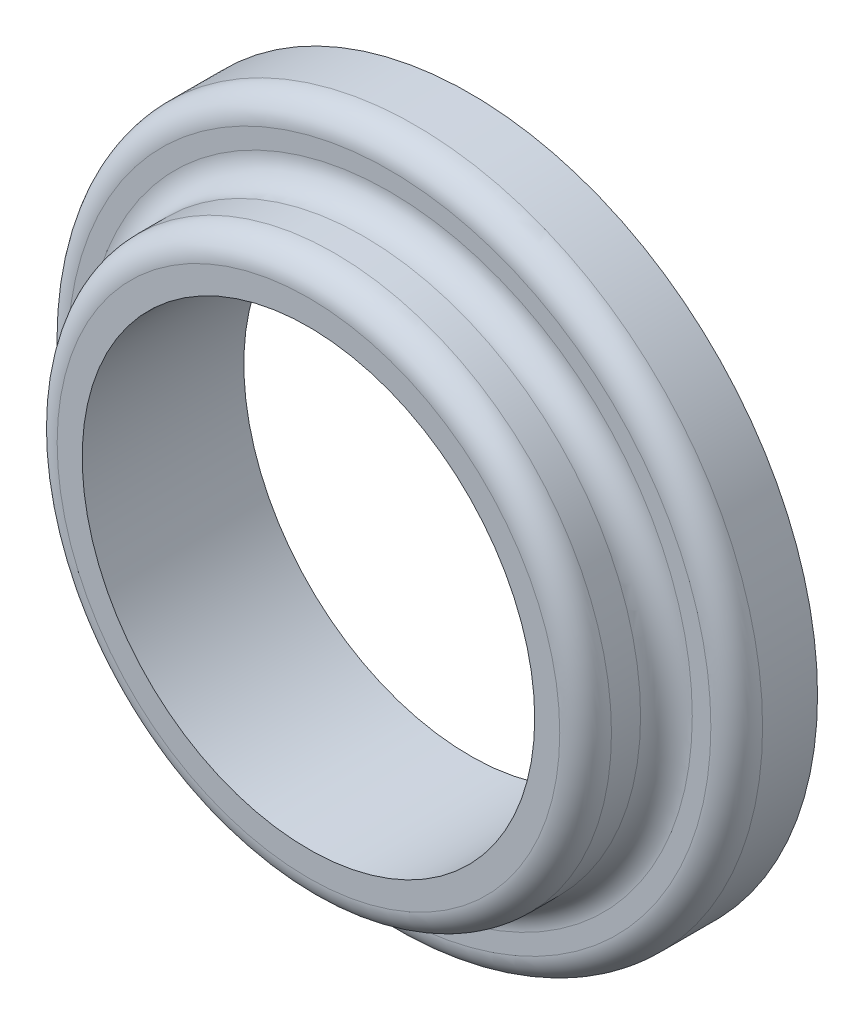
SolidWorks part; units mm, degrees
material "Nylon 101"
ref_plane "Front Plane" through (0, 0, 0) normal (0, 0, 1) x (1, 0, 0)
ref_plane "Top Plane" through (0, 0, 0) normal (0, 1, 0) x (1, 0, 0)
ref_plane "Right Plane" through (0, 0, 0) normal (1, 0, 0) x (0, 0, -1)
sketch "Sketch1" plane through (0, 0, 0) normal (0, 0, 1) x (1, 0, 0)
  circle A3 centre (-6.731, -165.7192) radius 6.8263
  circle A4 centre (-6.731, -165.7192) radius 4.445
  dimension "D1" = 2.3812
extrude "Boss-Extrude1" add sketch "Sketch1" along normal blind 1.5875
sketch "Sketch2" plane through (0, 0, 1.5875) normal (0, 0, 1) x (1, 0, 0)
  circle A0 centre (-6.731, -165.7192) radius 4.445 construction
  circle A1 centre (-6.731, -165.7192) radius 4.445
extrude "Extrude-Thin1" add sketch "Sketch2" along normal blind 1.5875 thin
fillet "Fillet1" radius 0.508 3 edges at (0.0953, -165.7192, 1.5875) (-1.286, -165.7192, 1.5875) (-1.286, -165.7192, 3.175)
